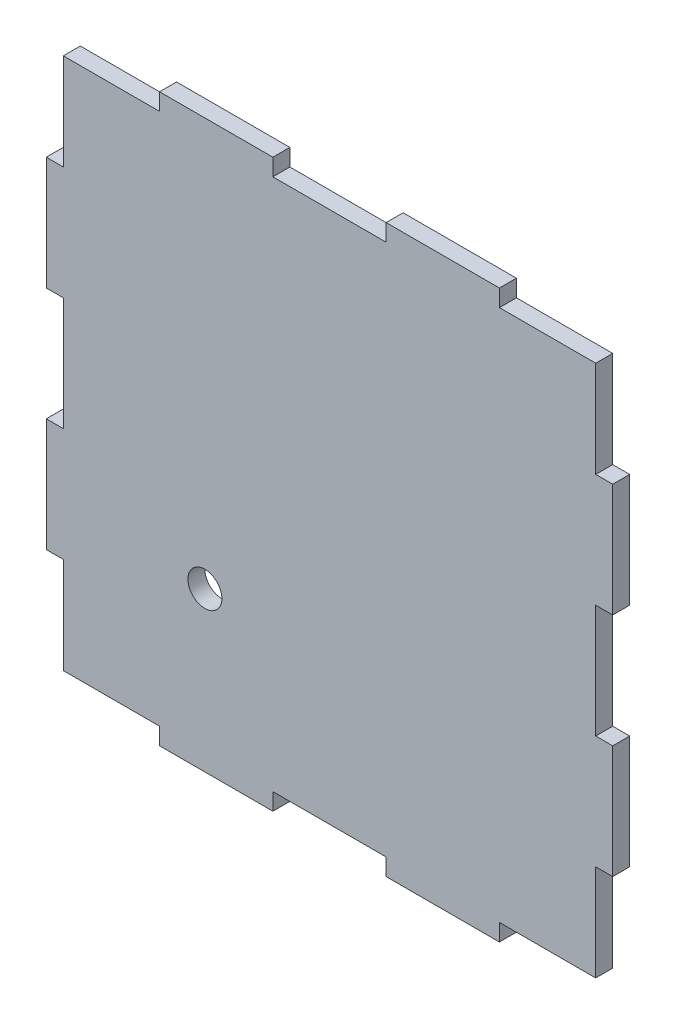
SolidWorks part; units mm, degrees
material "玻璃"
ref_plane "前视基准面" through (0, 0, 0) normal (0, 0, 1) x (1, 0, 0)
ref_plane "上视基准面" through (0, 0, 0) normal (0, 1, 0) x (1, 0, 0)
ref_plane "右视基准面" through (0, 0, 0) normal (1, 0, 0) x (0, 0, -1)
sketch "草图1" plane through (0, 0, 0) normal (0, 0, 1) x (1, 0, 0)
  line L0 (-109.1725, 0) -> (179.0942, 0) construction
  line L1 (0, 126.2991) -> (0, -137.7518) construction
  line L21 (-10, 47) -> (10, 47)
  line L39 (10, 47) -> (10, 50)
  line L40 (10, 50) -> (30, 50)
  line L41 (30, 50) -> (30, 47)
  line L42 (30, 47) -> (47, 47)
  line L43 (0, 0) -> (47, 47) construction
  line L44 (47, 30) -> (47, 47)
  line L45 (50, 30) -> (47, 30)
  line L46 (50, 10) -> (50, 30)
  line L47 (47, 10) -> (50, 10)
  line L48 (47, -10) -> (47, 10)
  line L49 (0, 0) -> (-47, 47) construction
  line L50 (-47, -10) -> (-47, 10)
  line L51 (-47, 10) -> (-50, 10)
  line L52 (-50, 10) -> (-50, 30)
  line L53 (-50, 30) -> (-47, 30)
  line L54 (-47, 30) -> (-47, 47)
  line L55 (-30, 47) -> (-47, 47)
  line L56 (-30, 50) -> (-30, 47)
  line L57 (-10, 50) -> (-30, 50)
  line L58 (-10, 47) -> (-10, 50)
  line L59 (0, 0) -> (-47, -47) construction
  line L61 (-10, -47) -> (-10, -50)
  line L62 (-10, -50) -> (-30, -50)
  line L63 (-30, -50) -> (-30, -47)
  line L64 (-30, -47) -> (-47, -47)
  line L65 (-47, -30) -> (-47, -47)
  line L66 (-50, -30) -> (-47, -30)
  line L67 (-50, -10) -> (-50, -30)
  line L68 (-47, -10) -> (-50, -10)
  line L69 (47, -10) -> (50, -10)
  line L70 (50, -10) -> (50, -30)
  line L71 (50, -30) -> (47, -30)
  line L72 (47, -30) -> (47, -47)
  line L73 (30, -47) -> (47, -47)
  line L74 (30, -50) -> (30, -47)
  line L75 (10, -50) -> (30, -50)
  line L76 (10, -47) -> (10, -50)
  line L77 (-10, -47) -> (10, -47)
  circle A0 centre (-22.0019, -22.0019) radius 3
  point P26 (0, 47)
  point P36 (-47, 0)
  point P37 (47, 0)
  point P44 (0, -47)
  dimension "D1" = 20
  dimension "D2" = 10
  dimension "D3" = 17
  dimension "D4" = 3
  dimension "D5" = 3
extrude "凸台-拉伸2" add sketch "草图1" along normal blind 3 contours A0 | L61 L62 L63 L64 L65 L66 L67 L68 L50 L51 L52 L53 L54 L55 L56 L57 L58 L21 L39 L40 L41 L42 L44 L45 L46 L47 L48 L69 L70 L71 L72 L73 L74 L75 L76 L77
